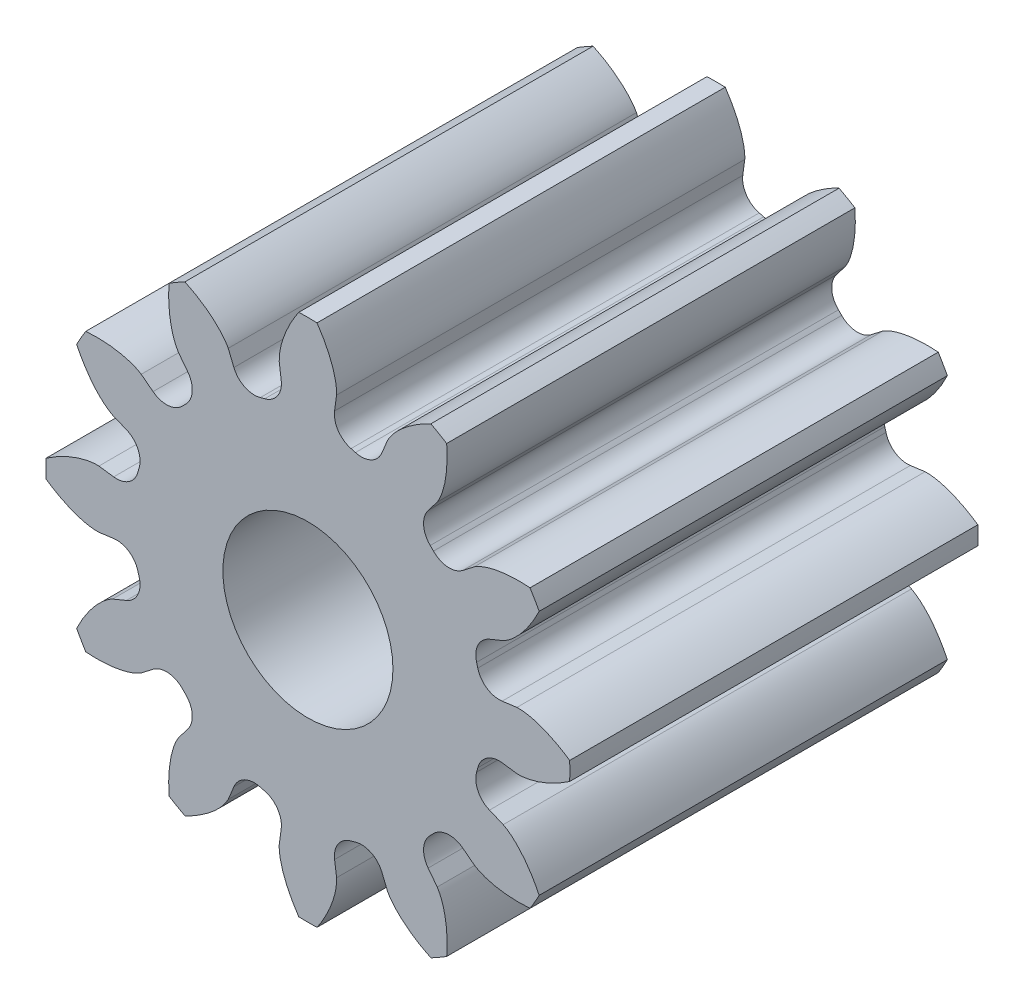
SolidWorks part; units mm, degrees
ref_plane "Front Plane" through (0, 0, 0) normal (0, 0, 1) x (1, 0, 0)
ref_plane "Top Plane" through (0, 0, 0) normal (0, 1, 0) x (1, 0, 0)
ref_plane "Right Plane" through (0, 0, 0) normal (1, 0, 0) x (0, 0, -1)
ref_plane "Plane1" through (0, 0, 0) normal (0, 0, -1) x (-1, 0, 0)
sketch "Sketch1" plane through (0, 0, 0) normal (0, 0, -1) x (-1, 0, 0)
  line L0 (-1.4138, -1.821) -> (-1.5209, -1.9599)
  line L1 (-0.9369, -2.2971) -> (-0.8702, -2.1349)
  line L2 (-0.3139, -2.284) -> (-0.3372, -2.4578)
  line L3 (0.3372, -2.4578) -> (0.3139, -2.284)
  line L4 (0.8702, -2.1349) -> (0.9369, -2.2971)
  line L5 (1.5209, -1.9599) -> (1.4138, -1.821)
  line L6 (1.821, -1.4138) -> (1.9599, -1.5209)
  line L7 (2.2971, -0.9369) -> (2.1349, -0.8702)
  line L8 (2.284, -0.3139) -> (2.4578, -0.3372)
  line L9 (2.4578, 0.3372) -> (2.284, 0.3139)
  line L10 (2.1349, 0.8702) -> (2.2971, 0.9369)
  line L11 (1.9599, 1.5209) -> (1.821, 1.4138)
  line L12 (1.4138, 1.821) -> (1.5209, 1.9599)
  line L13 (0.9369, 2.2971) -> (0.8702, 2.1349)
  line L14 (0.3139, 2.284) -> (0.3372, 2.4578)
  line L15 (-0.3372, 2.4578) -> (-0.3139, 2.284)
  line L16 (-0.8702, 2.1349) -> (-0.9369, 2.2971)
  line L17 (-1.5209, 1.9599) -> (-1.4138, 1.821)
  line L18 (-1.821, 1.4138) -> (-1.9599, 1.5209)
  line L19 (-2.2971, 0.9369) -> (-2.1349, 0.8702)
  line L20 (-2.284, 0.3139) -> (-2.4578, 0.3372)
  line L21 (-2.4578, -0.3372) -> (-2.284, -0.3139)
  line L22 (-2.1349, -0.8702) -> (-2.2971, -0.9369)
  line L23 (-1.9599, -1.5209) -> (-1.821, -1.4138)
  arc A0 (-1.4765, -1.4383) -> (-1.4383, -1.4765) centre (0, 0) ccw
  arc A1 (-1.4383, -1.4765) -> (-1.4138, -1.821) centre (-1.6195, -1.6625) cw
  arc A2 (-1.6321, -2.612) -> (-1.446, -2.7194) centre (0, 0) ccw
  arc A3 (-0.8702, -2.1349) -> (-0.5595, -1.9838) centre (-0.63, -2.2338) cw
  arc A4 (-0.5595, -1.9838) -> (-0.5074, -1.9978) centre (0, 0) ccw
  arc A5 (-0.5074, -1.9978) -> (-0.3139, -2.284) centre (-0.5713, -2.2495) cw
  arc A6 (-0.1074, -3.0781) -> (0.1074, -3.0781) centre (0, 0) ccw
  arc A7 (0.3139, -2.284) -> (0.5074, -1.9978) centre (0.5713, -2.2495) cw
  arc A8 (0.5074, -1.9978) -> (0.5595, -1.9838) centre (0, 0) ccw
  arc A9 (0.5595, -1.9838) -> (0.8702, -2.1349) centre (0.63, -2.2338) cw
  arc A10 (1.446, -2.7194) -> (1.6321, -2.612) centre (0, 0) ccw
  arc A11 (1.4138, -1.821) -> (1.4383, -1.4765) centre (1.6195, -1.6625) cw
  arc A12 (1.4383, -1.4765) -> (1.4765, -1.4383) centre (0, 0) ccw
  arc A13 (1.4765, -1.4383) -> (1.821, -1.4138) centre (1.6625, -1.6195) cw
  arc A14 (2.612, -1.6321) -> (2.7194, -1.446) centre (0, 0) ccw
  arc A15 (2.1349, -0.8702) -> (1.9838, -0.5595) centre (2.2338, -0.63) cw
  arc A16 (1.9838, -0.5595) -> (1.9978, -0.5074) centre (0, 0) ccw
  arc A17 (1.9978, -0.5074) -> (2.284, -0.3139) centre (2.2495, -0.5713) cw
  arc A18 (3.0781, -0.1074) -> (3.0781, 0.1074) centre (0, 0) ccw
  arc A19 (2.284, 0.3139) -> (1.9978, 0.5074) centre (2.2495, 0.5713) cw
  arc A20 (1.9978, 0.5074) -> (1.9838, 0.5595) centre (0, 0) ccw
  arc A21 (1.9838, 0.5595) -> (2.1349, 0.8702) centre (2.2338, 0.63) cw
  arc A22 (2.7194, 1.446) -> (2.612, 1.6321) centre (0, 0) ccw
  arc A23 (1.821, 1.4138) -> (1.4765, 1.4383) centre (1.6625, 1.6195) cw
  arc A24 (1.4765, 1.4383) -> (1.4383, 1.4765) centre (0, 0) ccw
  arc A25 (1.4383, 1.4765) -> (1.4138, 1.821) centre (1.6195, 1.6625) cw
  arc A26 (1.6321, 2.612) -> (1.446, 2.7194) centre (0, 0) ccw
  arc A27 (0.8702, 2.1349) -> (0.5595, 1.9838) centre (0.63, 2.2338) cw
  arc A28 (0.5595, 1.9838) -> (0.5074, 1.9978) centre (0, 0) ccw
  arc A29 (0.5074, 1.9978) -> (0.3139, 2.284) centre (0.5713, 2.2495) cw
  arc A30 (0.1074, 3.0781) -> (-0.1074, 3.0781) centre (0, 0) ccw
  arc A31 (-0.3139, 2.284) -> (-0.5074, 1.9978) centre (-0.5713, 2.2495) cw
  arc A32 (-0.5074, 1.9978) -> (-0.5595, 1.9838) centre (0, 0) ccw
  arc A33 (-0.5595, 1.9838) -> (-0.8702, 2.1349) centre (-0.63, 2.2338) cw
  arc A34 (-1.446, 2.7194) -> (-1.6321, 2.612) centre (0, 0) ccw
  arc A35 (-1.4138, 1.821) -> (-1.4383, 1.4765) centre (-1.6195, 1.6625) cw
  arc A36 (-1.4383, 1.4765) -> (-1.4765, 1.4383) centre (0, 0) ccw
  arc A37 (-1.4765, 1.4383) -> (-1.821, 1.4138) centre (-1.6625, 1.6195) cw
  arc A38 (-2.612, 1.6321) -> (-2.7194, 1.446) centre (0, 0) ccw
  arc A39 (-2.1349, 0.8702) -> (-1.9838, 0.5595) centre (-2.2338, 0.63) cw
  arc A40 (-1.9838, 0.5595) -> (-1.9978, 0.5074) centre (0, 0) ccw
  arc A41 (-1.9978, 0.5074) -> (-2.284, 0.3139) centre (-2.2495, 0.5713) cw
  arc A42 (-3.0781, 0.1074) -> (-3.0781, -0.1074) centre (0, 0) ccw
  arc A43 (-2.284, -0.3139) -> (-1.9978, -0.5074) centre (-2.2495, -0.5713) cw
  arc A44 (-1.9978, -0.5074) -> (-1.9838, -0.5595) centre (0, 0) ccw
  arc A45 (-1.9838, -0.5595) -> (-2.1349, -0.8702) centre (-2.2338, -0.63) cw
  arc A46 (-2.7194, -1.446) -> (-2.612, -1.6321) centre (0, 0) ccw
  arc A47 (-1.821, -1.4138) -> (-1.4765, -1.4383) centre (-1.6625, -1.6195) cw
  circle A48 centre (0, 0) radius 1
  ellipse E0 centre (-1.3171, -2.5743) end of major axis (-1.3674, -1.8483) minor radius 0.3169 (-1.5209, -1.9599) -> (-1.6321, -2.612) ccw
  ellipse E1 centre (-1.5708, -2.4278) end of major axis (-2.2247, -2.7473) minor radius 0.3169 (-1.446, -2.7194) -> (-0.9369, -2.2971) ccw
  ellipse E2 centre (0.1465, -2.888) end of major axis (0.553, -3.4915) minor radius 0.3169 (-0.3372, -2.4578) -> (-0.1074, -3.0781) ccw
  ellipse E3 centre (-0.1465, -2.888) end of major axis (-0.553, -3.4915) minor radius 0.3169 (0.1074, -3.0781) -> (0.3372, -2.4578) ccw
  ellipse E4 centre (1.5708, -2.4278) end of major axis (0.917, -2.1083) minor radius 0.3169 (0.9369, -2.2971) -> (1.446, -2.7194) ccw
  ellipse E5 centre (1.3171, -2.5743) end of major axis (1.2669, -3.3003) minor radius 0.3169 (1.6321, -2.612) -> (1.5209, -1.9599) ccw
  ellipse E6 centre (2.5743, -1.3171) end of major axis (1.8483, -1.3674) minor radius 0.3169 (1.9599, -1.5209) -> (2.612, -1.6321) ccw
  ellipse E7 centre (2.4278, -1.5708) end of major axis (2.7473, -2.2247) minor radius 0.3169 (2.7194, -1.446) -> (2.2971, -0.9369) ccw
  ellipse E8 centre (2.888, 0.1465) end of major axis (2.2844, -0.26) minor radius 0.3169 (2.4578, -0.3372) -> (3.0781, -0.1074) ccw
  ellipse E9 centre (2.888, -0.1465) end of major axis (2.2844, 0.26) minor radius 0.3169 (3.0781, 0.1074) -> (2.4578, 0.3372) ccw
  ellipse E10 centre (2.4278, 1.5708) end of major axis (2.7473, 2.2247) minor radius 0.3169 (2.2971, 0.9369) -> (2.7194, 1.446) ccw
  ellipse E11 centre (2.5743, 1.3171) end of major axis (1.8483, 1.3674) minor radius 0.3169 (2.612, 1.6321) -> (1.9599, 1.5209) ccw
  ellipse E12 centre (1.3171, 2.5743) end of major axis (1.2669, 3.3003) minor radius 0.3169 (1.5209, 1.9599) -> (1.6321, 2.612) ccw
  ellipse E13 centre (1.5708, 2.4278) end of major axis (0.917, 2.1083) minor radius 0.3169 (1.446, 2.7194) -> (0.9369, 2.2971) ccw
  ellipse E14 centre (-0.1465, 2.888) end of major axis (-0.553, 3.4915) minor radius 0.3169 (0.3372, 2.4578) -> (0.1074, 3.0781) ccw
  ellipse E15 centre (0.1465, 2.888) end of major axis (-0.26, 2.2844) minor radius 0.3169 (-0.1074, 3.0781) -> (-0.3372, 2.4578) ccw
  ellipse E16 centre (-1.5708, 2.4278) end of major axis (-2.2247, 2.7473) minor radius 0.3169 (-0.9369, 2.2971) -> (-1.446, 2.7194) ccw
  ellipse E17 centre (-1.3171, 2.5743) end of major axis (-1.2669, 3.3003) minor radius 0.3169 (-1.6321, 2.612) -> (-1.5209, 1.9599) ccw
  ellipse E18 centre (-2.5743, 1.3171) end of major axis (-3.3003, 1.2669) minor radius 0.3169 (-1.9599, 1.5209) -> (-2.612, 1.6321) ccw
  ellipse E19 centre (-2.4278, 1.5708) end of major axis (-2.7473, 2.2247) minor radius 0.3169 (-2.7194, 1.446) -> (-2.2971, 0.9369) ccw
  ellipse E20 centre (-2.888, -0.1465) end of major axis (-3.4915, -0.553) minor radius 0.3169 (-2.4578, 0.3372) -> (-3.0781, 0.1074) ccw
  ellipse E21 centre (-2.888, 0.1465) end of major axis (-3.4915, 0.553) minor radius 0.3169 (-3.0781, -0.1074) -> (-2.4578, -0.3372) ccw
  ellipse E22 centre (-2.4278, -1.5708) end of major axis (-2.1083, -0.917) minor radius 0.3169 (-2.2971, -0.9369) -> (-2.7194, -1.446) ccw
  ellipse E23 centre (-2.5743, -1.3171) end of major axis (-3.3003, -1.2669) minor radius 0.3169 (-2.612, -1.6321) -> (-1.9599, -1.5209) ccw
  point P6 (-1.3171, -2.5743)
  point P7 (-1.6333, -2.5962)
  point P8 (-1.3674, -1.8483)
  point P9 (-1.5209, -1.9599)
  point P10 (-1.6321, -2.612)
  point P11 (-1.6211, -2.2612)
  point P12 (-1.0131, -2.8874)
  point P20 (-1.5708, -2.4278)
  point P21 (-2.2247, -2.7473)
  point P22 (-1.4317, -2.7125)
  point P23 (-1.446, -2.7194)
  point P24 (-0.9369, -2.2971)
  point P25 (-1.1477, -2.5346)
  point P26 (-1.994, -2.321)
  point P40 (0.1465, -2.888)
  point P41 (-0.1164, -3.065)
  point P42 (-0.26, -2.2844)
  point P43 (-0.3372, -2.4578)
  point P44 (-0.1074, -3.0781)
  point P45 (-0.2734, -2.7688)
  point P46 (0.5663, -3.0071)
  point P54 (-0.1465, -2.888)
  point P55 (-0.4093, -2.7109)
  point P56 (-0.553, -3.4915)
  point P57 (0.1074, -3.0781)
  point P58 (0.3372, -2.4578)
  point P59 (0.2734, -2.7688)
  point P60 (-0.5663, -3.0071)
  point P74 (1.5708, -2.4278)
  point P75 (0.917, -2.1083)
  point P76 (1.71, -2.1431)
  point P77 (0.9369, -2.2971)
  point P78 (1.446, -2.7194)
  point P79 (1.1477, -2.5346)
  point P80 (1.994, -2.321)
  point P88 (1.3171, -2.5743)
  point P89 (1.001, -2.5524)
  point P90 (1.2669, -3.3003)
  point P91 (1.6321, -2.612)
  point P92 (1.5209, -1.9599)
  point P93 (1.6211, -2.2612)
  point P94 (1.0131, -2.8874)
  point P108 (2.5743, -1.3171)
  point P109 (1.8483, -1.3674)
  point P110 (2.5524, -1.001)
  point P111 (1.9599, -1.5209)
  point P112 (2.612, -1.6321)
  point P113 (2.2612, -1.6211)
  point P114 (2.8874, -1.0131)
  point P122 (2.4278, -1.5708)
  point P123 (2.1431, -1.71)
  point P124 (2.7473, -2.2247)
  point P125 (2.7194, -1.446)
  point P126 (2.2971, -0.9369)
  point P127 (2.5346, -1.1477)
  point P128 (2.321, -1.994)
  point P142 (2.888, 0.1465)
  point P143 (2.2844, -0.26)
  point P144 (2.7109, 0.4093)
  point P145 (2.4578, -0.3372)
  point P146 (3.0781, -0.1074)
  point P147 (2.7688, -0.2734)
  point P148 (3.0071, 0.5663)
  point P156 (2.888, -0.1465)
  point P157 (2.2844, 0.26)
  point P158 (2.7109, -0.4093)
  point P159 (3.0781, 0.1074)
  point P160 (2.4578, 0.3372)
  point P161 (2.7688, 0.2734)
  point P162 (3.0071, -0.5663)
  point P176 (2.4278, 1.5708)
  point P177 (2.1431, 1.71)
  point P178 (2.7473, 2.2247)
  point P179 (2.2971, 0.9369)
  point P180 (2.7194, 1.446)
  point P181 (2.5346, 1.1477)
  point P182 (2.321, 1.994)
  point P190 (2.5743, 1.3171)
  point P191 (1.8483, 1.3674)
  point P192 (2.5524, 1.001)
  point P193 (2.612, 1.6321)
  point P194 (1.9599, 1.5209)
  point P195 (2.2612, 1.6211)
  point P196 (2.8874, 1.0131)
  point P210 (1.3171, 2.5743)
  point P211 (1.001, 2.5524)
  point P212 (1.2669, 3.3003)
  point P213 (1.5209, 1.9599)
  point P214 (1.6321, 2.612)
  point P215 (1.6211, 2.2612)
  point P216 (1.0131, 2.8874)
  point P224 (1.5708, 2.4278)
  point P225 (0.917, 2.1083)
  point P226 (1.71, 2.1431)
  point P227 (1.446, 2.7194)
  point P228 (0.9369, 2.2971)
  point P229 (1.1477, 2.5346)
  point P230 (1.994, 2.321)
  point P244 (-0.1465, 2.888)
  point P245 (-0.4093, 2.7109)
  point P246 (-0.553, 3.4915)
  point P247 (0.3372, 2.4578)
  point P248 (0.1074, 3.0781)
  point P249 (0.2734, 2.7688)
  point P250 (-0.5663, 3.0071)
  point P258 (0.1465, 2.888)
  point P259 (-0.1164, 3.065)
  point P260 (-0.26, 2.2844)
  point P261 (-0.1074, 3.0781)
  point P262 (-0.3372, 2.4578)
  point P263 (-0.2734, 2.7688)
  point P264 (0.5663, 3.0071)
  point P278 (-1.5708, 2.4278)
  point P279 (-2.2247, 2.7473)
  point P280 (-1.4317, 2.7125)
  point P281 (-0.9369, 2.2971)
  point P282 (-1.446, 2.7194)
  point P283 (-1.1477, 2.5346)
  point P284 (-1.994, 2.321)
  point P292 (-1.3171, 2.5743)
  point P293 (-1.6333, 2.5962)
  point P294 (-1.3674, 1.8483)
  point P295 (-1.6321, 2.612)
  point P296 (-1.5209, 1.9599)
  point P297 (-1.6211, 2.2612)
  point P298 (-1.0131, 2.8874)
  point P312 (-2.5743, 1.3171)
  point P313 (-3.3003, 1.2669)
  point P314 (-2.5962, 1.6333)
  point P315 (-1.9599, 1.5209)
  point P316 (-2.612, 1.6321)
  point P317 (-2.2612, 1.6211)
  point P318 (-2.8874, 1.0131)
  point P326 (-2.4278, 1.5708)
  point P327 (-2.7125, 1.4317)
  point P328 (-2.1083, 0.917)
  point P329 (-2.7194, 1.446)
  point P330 (-2.2971, 0.9369)
  point P331 (-2.5346, 1.1477)
  point P332 (-2.321, 1.994)
  point P346 (-2.888, -0.1465)
  point P347 (-3.4915, -0.553)
  point P348 (-3.065, 0.1164)
  point P349 (-2.4578, 0.3372)
  point P350 (-3.0781, 0.1074)
  point P351 (-2.7688, 0.2734)
  point P352 (-3.0071, -0.5663)
  point P360 (-2.888, 0.1465)
  point P361 (-3.4915, 0.553)
  point P362 (-3.065, -0.1164)
  point P363 (-3.0781, -0.1074)
  point P364 (-2.4578, -0.3372)
  point P365 (-2.7688, -0.2734)
  point P366 (-3.0071, 0.5663)
  point P380 (-2.4278, -1.5708)
  point P381 (-2.7125, -1.4317)
  point P382 (-2.1083, -0.917)
  point P383 (-2.2971, -0.9369)
  point P384 (-2.7194, -1.446)
  point P385 (-2.5346, -1.1477)
  point P386 (-2.321, -1.994)
  point P394 (-2.5743, -1.3171)
  point P395 (-3.3003, -1.2669)
  point P396 (-2.5962, -1.6333)
  point P397 (-2.612, -1.6321)
  point P398 (-1.9599, -1.5209)
  point P399 (-2.2612, -1.6211)
  point P400 (-2.8874, -1.0131)
extrude "Boss-Extrude1" add sketch "Sketch1" against normal blind 4.8
